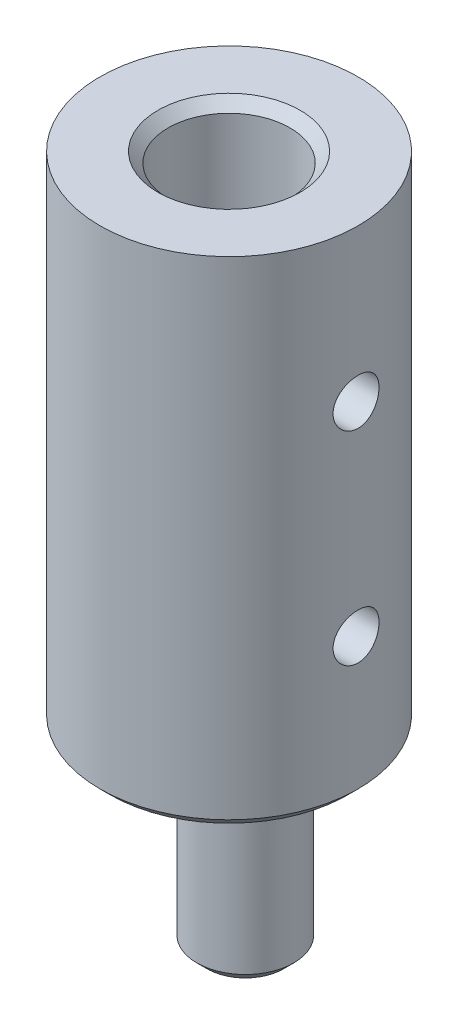
SolidWorks part; units mm, degrees
ref_plane "Front Plane" through (0, 0, 0) normal (0, 0, 1) x (1, 0, 0)
ref_plane "Top Plane" through (0, 0, 0) normal (0, 1, 0) x (1, 0, 0)
ref_plane "Right Plane" through (0, 0, 0) normal (1, 0, 0) x (0, 0, -1)
sketch "Sketch1" plane through (0, 0, 0) normal (0, 1, 0) x (1, 0, 0)
  circle A0 centre (0, 0) radius 6.35
  dimension "D1" = 12.7
extrude "Boss-Extrude1" add sketch "Sketch1" along normal blind 24.5
sketch "Sketch2" plane through (0, 24.5, 0) normal (0, 1, 0) x (1, 0, 0)
  circle A0 centre (0, 0) radius 3
  dimension "D1" = 6
extrude "Cut-Extrude1" cut sketch "Sketch2" against normal blind 21.6
ref_plane "Plane1" through (6.35, 0, 0) normal (1, 0, 0) x (0, 0, -1)
hole_wizard "#4-40 Tapped Hole1" positions "Sketch3" profile "Sketch4" tap size "#4-40" standard "ANSI Inch" end condition through all
sketch "Sketch3" plane through (6.35, 0, 0) normal (1, 0, 0) x (0, 0, -1)
  line L0 (-6.35, 0) -> (6.35, 0) construction
  point P0 (0, 17)
  point P2 (0, 7)
  dimension "D1" = 7
  dimension "D2" = 10
sketch "Sketch4" plane through (6.35, 17, 0) normal (0, 1, 0) x (0, 0, -1)
  line L0 (0, 0) -> (0, 12.7)
  line L1 (0, 12.7) -> (1.1303, 12.7)
  line L2 (1.1303, 12.7) -> (1.1303, 0)
  line L5 (1.1303, 0) -> (0, 0)
  line L11 (0, -6.35) -> (0, 107.95) construction
  dimension "Thru Tap Drill Dia." = 2.2606
  dimension "Thru Tap Drill Depth" = 12.7
cosmetic thread "Hole Thread1" parameters "D2"=2.8448
cosmetic thread "Hole Thread2" parameters "D2"=2.8448
sketch "Sketch5" plane through (0, 0, 0) normal (0, -1, 0) x (-1, 0, 0)
  line L0 (-6.985, 0) -> (6.985, 0) construction
  line L1 (0, 6.985) -> (0, -6.985) construction
  circle A0 centre (-0.8, 0) radius 2.3813
  dimension "D1" = 4.7625
  dimension "D2" = 0.8
extrude "Boss-Extrude2" add sketch "Sketch5" along normal blind 9
chamfer "Chamfer2" distance 0.5 angle 45 4 edges at (0.8, -9, -2.3813) (0, 0, 6.35) (0.8, 0, -2.3813) (0, 24.5, 3)
